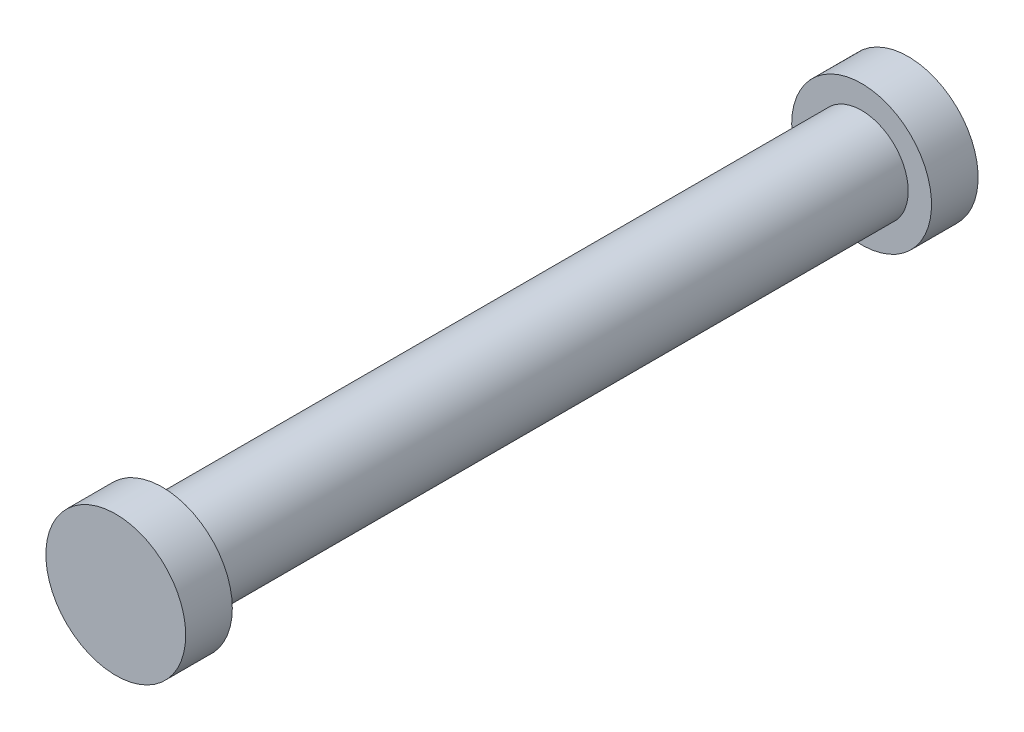
SolidWorks part; units mm, degrees
ref_plane "Front Plane" through (0, 0, 0) normal (0, 0, 1) x (1, 0, 0)
ref_plane "Top Plane" through (0, 0, 0) normal (0, 1, 0) x (1, 0, 0)
ref_plane "Right Plane" through (0, 0, 0) normal (1, 0, 0) x (0, 0, -1)
sketch "Sketch1" plane through (0, 0, 0) normal (0, 0, 1) x (1, 0, 0)
  circle A0 centre (0, 0) radius 6.35
  dimension "D1" = 12.7
extrude "Boss-Extrude1" add sketch "Sketch1" against normal blind 95.25
sketch "Sketch2" plane through (0, 0, 0) normal (0, 0, 1) x (1, 0, 0)
  circle A0 centre (0, 0) radius 9.525
  dimension "D1" = 19.05
extrude "Boss-Extrude2" add sketch "Sketch2" along normal blind 6.35
sketch "Sketch3" plane through (0, 0, -95.25) normal (0, 0, -1) x (-1, 0, 0)
  circle A0 centre (0, 0) radius 9.525
  dimension "D1" = 19.05
extrude "Boss-Extrude3" add sketch "Sketch3" along normal blind 6.35
